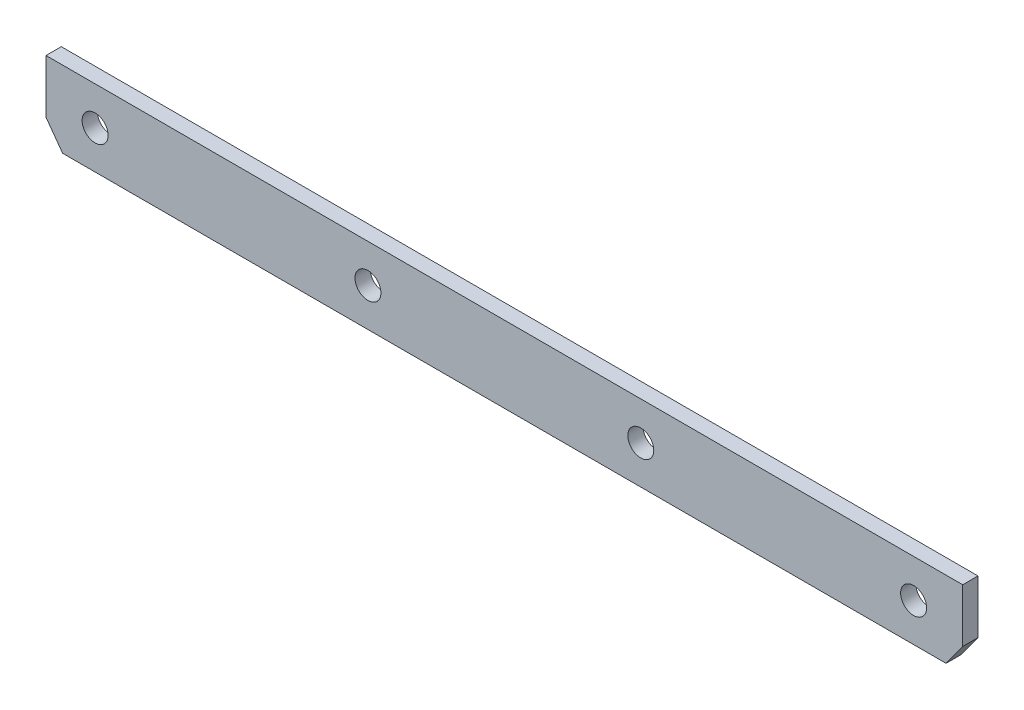
SolidWorks part; units mm, degrees
material "3.3315 (EN-AW 5005)"
ref_plane "Front Plane" through (0, 0, 0) normal (0, 0, 1) x (1, 0, 0)
ref_plane "Top Plane" through (0, 0, 0) normal (0, 1, 0) x (1, 0, 0)
ref_plane "Right Plane" through (0, 0, 0) normal (1, 0, 0) x (0, 0, -1)
sketch "Sketch1" plane through (0, 0, 0) normal (0, 0, 1) x (1, 0, 0)
  line L1 (135, -5) -> (-135, -5)
  line L2 (135, -5) -> (135, 5)
  line L3 (135, 5) -> (-135, 5)
  line L4 (-135, -5) -> (-135, 5)
  line L5 (135, -5) -> (-135, 5) construction
  line L6 (135, 5) -> (-135, -5) construction
  point P0 (0, 0)
  dimension "D1" = 270
  dimension "D2" = 10
extrude "Boss-Extrude1" add sketch "Sketch1" along normal blind 2
chamfer "Chamfer1" distance 2 angle 45 2 edges at (-135, -5, 1) (135, -5, 1)
hole_wizard "M3 Clearance Hole1" positions "Sketch2" profile "Sketch3" hole size "M3" standard "ISO" end condition through all
sketch "Sketch2" plane through (0, 0, 2) normal (0, 0, 1) x (1, 0, 0)
  line L0 (135, -3) -> (135, 5) construction
  line L1 (-133, -5) -> (133, -5) construction
  point P0 (125, 0)
  dimension "D1" = 10
  dimension "D2" = 5
sketch "Sketch3" plane through (125, 0, 2) normal (1, 0, 0) x (0, -1, 0)
  line L0 (0, 0) -> (0, 2)
  line L1 (0, 2) -> (1.7, 2)
  line L2 (1.7, 2) -> (1.7, 0)
  line L5 (1.7, 0) -> (0, 0)
  line L11 (0, -6.35) -> (0, 107.95) construction
  dimension "Thru Hole Dia." = 3.4
  dimension "Thru Hole Depth" = 2
pattern_linear "LPattern1" count 8 spacing 35.7143 along (-1, 0, 0) of "M3 Clearance Hole1"
sketch "Sketch4" plane through (0, 0, 0) normal (0, 0, -1) x (-1, 0, 0)
  line L0 (60, 5) -> (-60, 5)
  line L1 (-60, 5) -> (-60, -2)
  line L2 (-60, -2) -> (-57.8204, -5)
  line L3 (133, -5) -> (-133, -5) construction
  line L4 (-57.8204, -5) -> (57.8204, -5)
  line L5 (-135, 5) -> (135, 5) construction
  line L6 (0, -5) -> (0, 5) construction
  line L7 (60, -2) -> (57.8204, -5)
  line L8 (60, 5) -> (60, -2)
  point P9 (-44.527, -5)
  point P10 (-60, -0.8004)
  dimension "D1" = 120
  dimension "D2" = 144
  dimension "D3" = 3
extrude "Cut-Extrude-Thin1" cut sketch "Sketch4" against normal blind 10 thin
